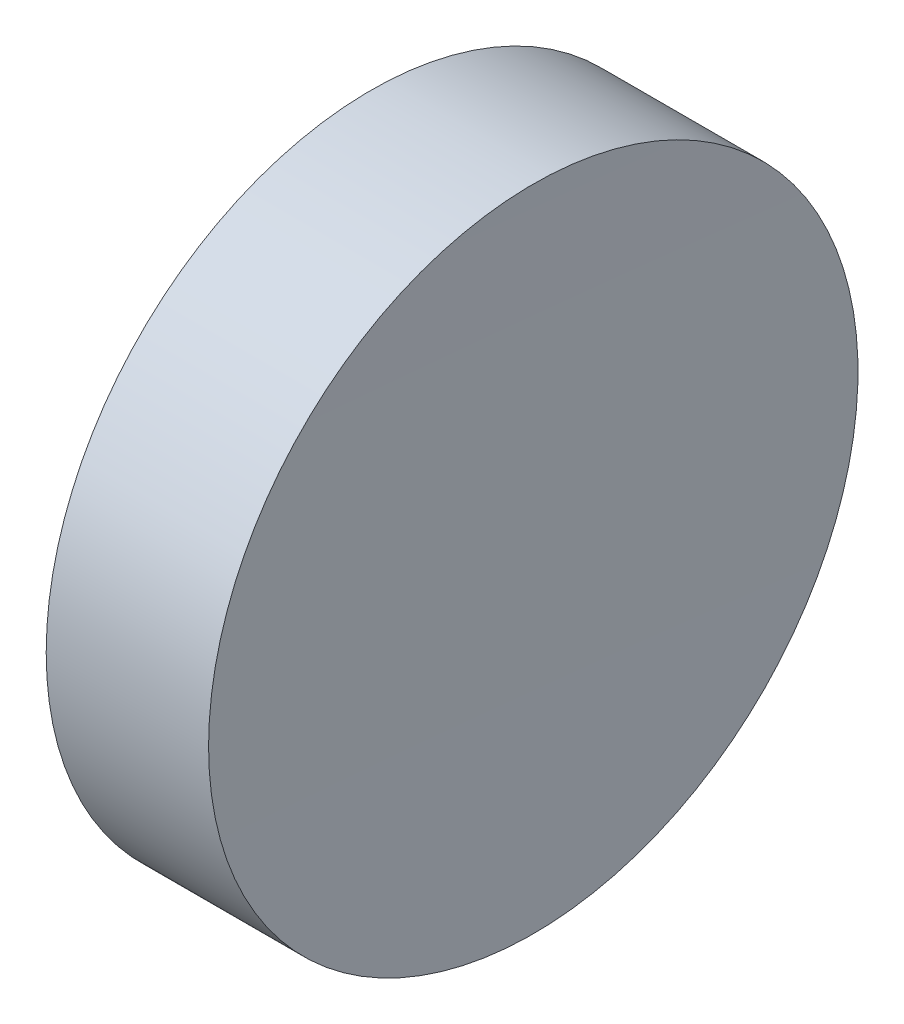
SolidWorks part; units mm, degrees
ref_plane "前视基准面" through (0, 0, 0) normal (0, 0, 1) x (1, 0, 0)
ref_plane "上视基准面" through (0, 0, 0) normal (0, 1, 0) x (1, 0, 0)
ref_plane "右视基准面" through (0, 0, 0) normal (1, 0, 0) x (0, 0, -1)
sketch "草图1" plane through (0, 0, 0) normal (0, 1, 0) x (1, 0, 0)
  line L0 (0, 0) -> (6.9328, 0) construction
  line L1 (0, 0) -> (6.27, 0)
  line L2 (0, 0) -> (0, 12.7)
  line L3 (0, 12.7) -> (6.3506, 12.7)
  arc A0 (6.3506, 12.7) -> (6.27, 0) centre (1006.27, 0) ccw
  dimension "D3" = 1000
  dimension "D1" = 6.27
  dimension "D2" = 12.7
revolve "旋转1" add sketch "草图1" angle 360 about L0
